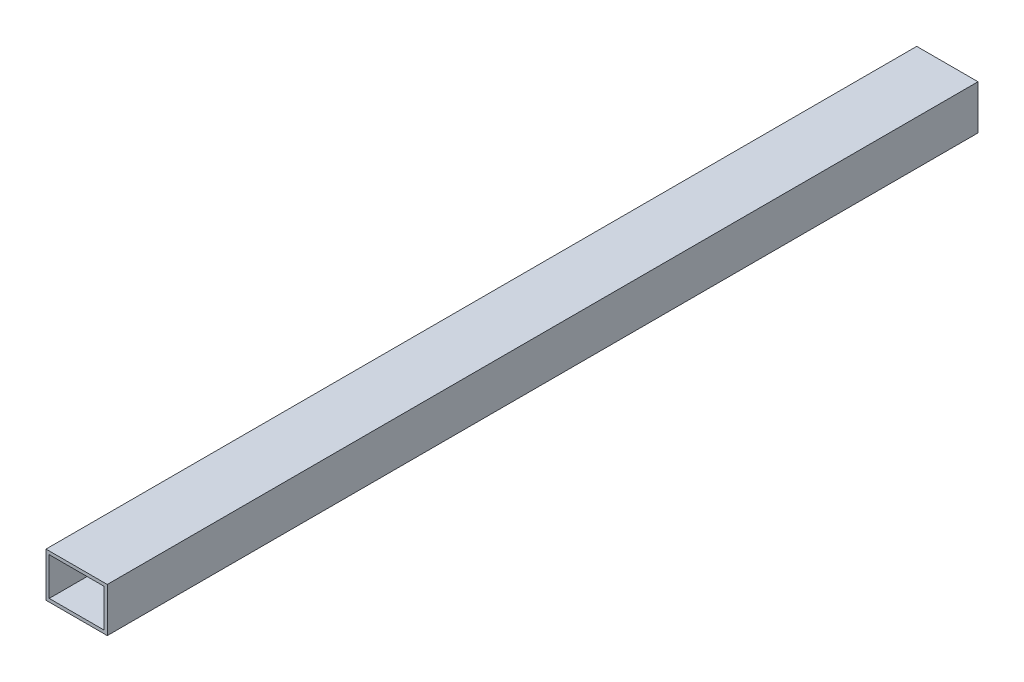
SolidWorks part; units mm, degrees
ref_plane "Front Plane" through (0, 0, 0) normal (0, 0, 1) x (1, 0, 0)
ref_plane "Top Plane" through (0, 0, 0) normal (0, 1, 0) x (1, 0, 0)
ref_plane "Right Plane" through (0, 0, 0) normal (1, 0, 0) x (0, 0, -1)
sketch "Sketch1" plane through (0, 0, 0) normal (0, 0, 1) x (1, 0, 0)
  line L1 (-32.9066, 27.067) -> (1.0934, 27.067)
  line L2 (-32.9066, 27.067) -> (-32.9066, 3.567)
  line L3 (-32.9066, 3.567) -> (1.0934, 3.567)
  line L4 (1.0934, 27.067) -> (1.0934, 3.567)
  line L5 (-34.9066, 29.067) -> (3.0934, 29.067)
  line L6 (-34.9066, 29.067) -> (-34.9066, 1.567)
  line L7 (-34.9066, 1.567) -> (3.0934, 1.567)
  line L8 (3.0934, 29.067) -> (3.0934, 1.567)
  dimension "D1" = 38
  dimension "D2" = 34
  dimension "D3" = 2
  dimension "D4" = 2
  dimension "D5" = 27.5
  dimension "D6" = 23.5
extrude "Boss-Extrude1" add sketch "Sketch1" along normal blind 540
